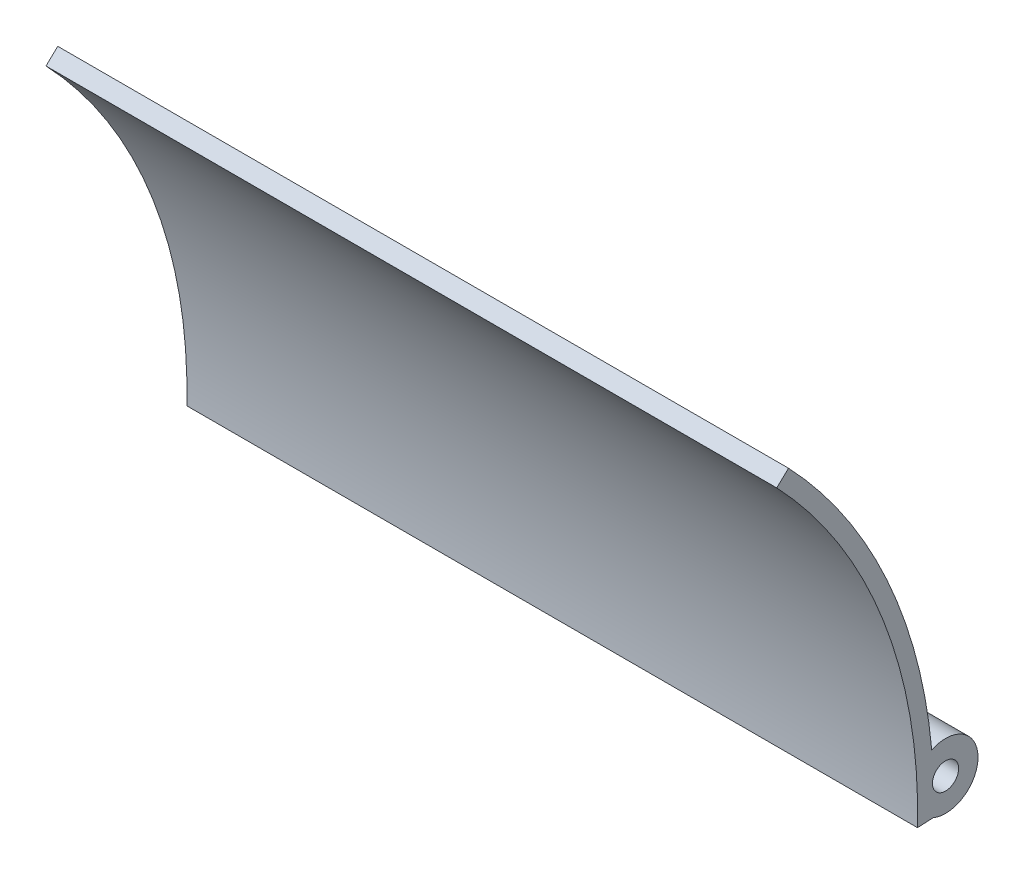
SolidWorks part; units mm, degrees
ref_plane "Front Plane" through (0, 0, 0) normal (0, 0, 1) x (1, 0, 0)
ref_plane "Top Plane" through (0, 0, 0) normal (0, 1, 0) x (1, 0, 0)
ref_plane "Right Plane" through (0, 0, 0) normal (1, 0, 0) x (0, 0, -1)
sketch "Sketch1" plane through (0, 0, 0) normal (1, 0, 0) x (0, 0, -1)
  line L1 (91.0874, 86.7682) -> (93.9837, 89.5272)
  line L2 (125.7629, -3.0541) -> (129.6165, -2.86)
  line L3 (129.2645, 11.7781) -> (129.6165, -2.86) construction
  arc A0 (125.7629, -3.0541) -> (91.0874, 86.7682) centre (0, 0) ccw
  arc A1 (129.2645, 11.7781) -> (93.9837, 89.5272) centre (0, 0) ccw
  arc A2 (129.7617, -3.1512) -> (93.9837, 89.5272) centre (0, 0) ccw construction
  arc A3 (129.2645, 11.7781) -> (129.6165, -2.86) centre (132.6646, 4.5365) cw
  circle A4 centre (132.6646, 4.5365) radius 3.225
  dimension "D1" = 125.8
  dimension "D4" = 6.45
  dimension "D5" = 8
  dimension "D2" = 45
  dimension "D3" = 4
extrude "Boss-Extrude1" add sketch "Sketch1" along normal blind 180
